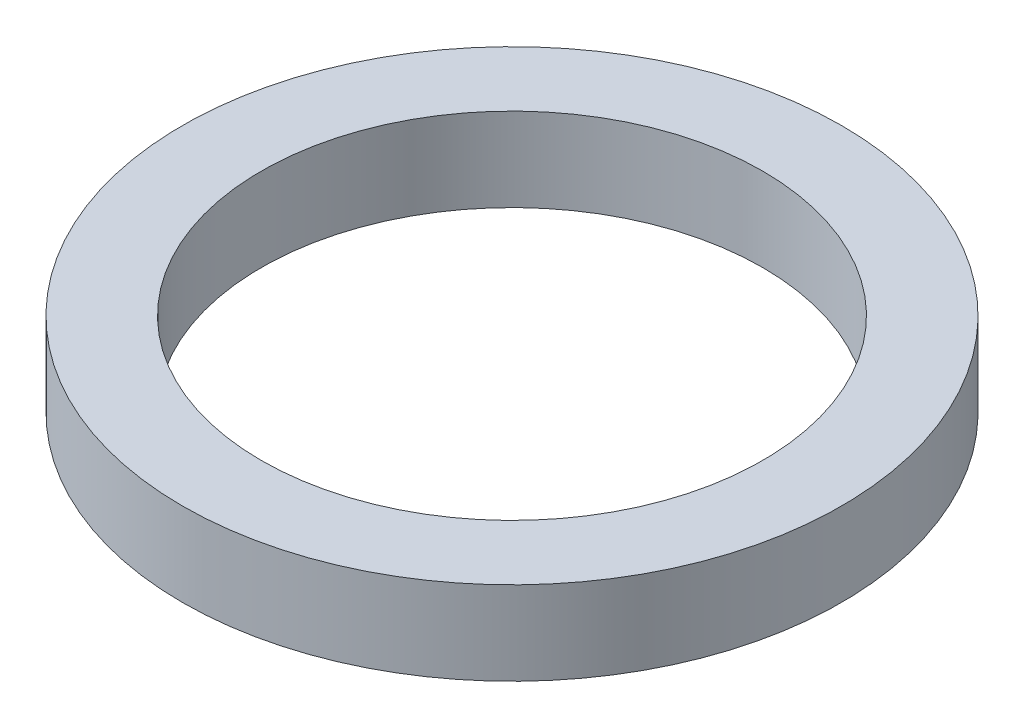
SolidWorks part; units mm, degrees
ref_plane "Front Plane" through (0, 0, 0) normal (0, 0, 1) x (1, 0, 0)
ref_plane "Top Plane" through (0, 0, 0) normal (0, 1, 0) x (1, 0, 0)
ref_plane "Right Plane" through (0, 0, 0) normal (1, 0, 0) x (0, 0, -1)
sketch "Sketch1" plane through (0, 0, 0) normal (0, 1, 0) x (1, 0, 0)
  circle A0 centre (0, 0) radius 4.7625
  circle A1 centre (0, 0) radius 6.2611
  dimension "D1" = 9.525
  dimension "D2" = 12.5222
extrude "Boss-Extrude1" add sketch "Sketch1" along normal blind 1.5875
